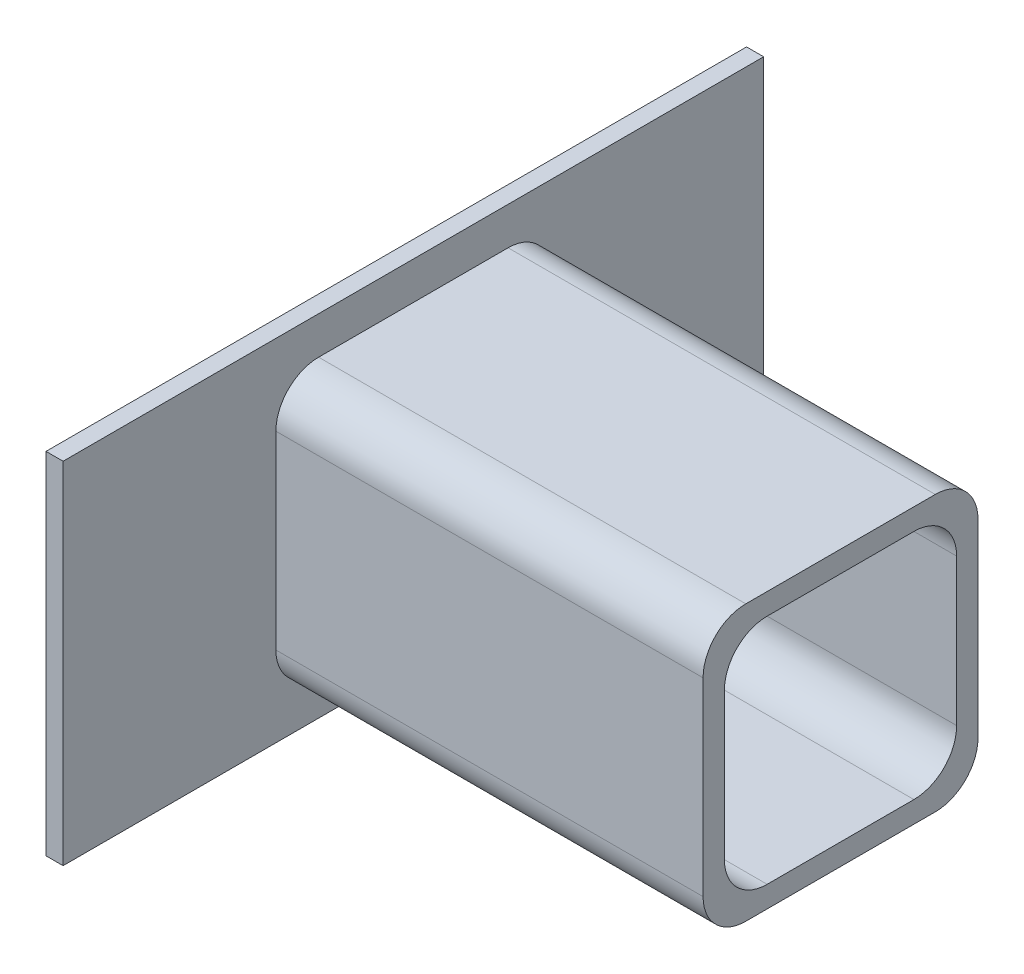
SolidWorks part; units mm, degrees
material "6061 Alloy"
ref_plane "Front Plane" through (0, 0, 0) normal (0, 0, 1) x (1, 0, 0)
ref_plane "Top Plane" through (0, 0, 0) normal (0, 1, 0) x (1, 0, 0)
ref_plane "Right Plane" through (0, 0, 0) normal (1, 0, 0) x (0, 0, -1)
sketch "Sketch1" plane through (0, 0, 0) normal (1, 0, 0) x (0, 0, -1)
  line L1 (-82, -41) -> (82, -41)
  line L2 (-82, -41) -> (-82, 41)
  line L3 (-82, 41) -> (82, 41)
  line L4 (82, -41) -> (82, 41)
  line L5 (-82, -41) -> (82, 41) construction
  line L6 (-82, 41) -> (82, -41) construction
  point P0 (0, 0)
  dimension "D1" = 82
  dimension "D2" = 164
extrude "Boss-Extrude1" add sketch "Sketch1" along normal blind 4
sketch "Sketch7" plane through (4, 0, 0) normal (1, 0, 0) x (0, 0, -1)
  line L1 (-17.18, -27.18) -> (17.18, -27.18)
  line L2 (-27.18, -17.18) -> (-27.18, 17.18)
  line L3 (-17.18, 27.18) -> (17.18, 27.18)
  line L4 (27.18, -17.18) -> (27.18, 17.18)
  line L5 (-27.18, -27.18) -> (27.18, 27.18) construction
  line L6 (-27.18, 27.18) -> (27.18, -27.18) construction
  line L7 (-22.18, -32.18) -> (22.18, -32.18)
  line L8 (-32.18, -22.18) -> (-32.18, 22.18)
  line L9 (-22.18, 32.18) -> (22.18, 32.18)
  line L10 (32.18, -22.18) -> (32.18, 22.18)
  line L11 (-32.18, -32.18) -> (32.18, 32.18) construction
  line L12 (-32.18, 32.18) -> (32.18, -32.18) construction
  arc A0 (22.18, -32.18) -> (32.18, -22.18) centre (22.18, -22.18) ccw
  arc A1 (22.18, 32.18) -> (32.18, 22.18) centre (22.18, 22.18) cw
  arc A2 (-32.18, 22.18) -> (-22.18, 32.18) centre (-22.18, 22.18) cw
  arc A3 (-22.18, -32.18) -> (-32.18, -22.18) centre (-22.18, -22.18) cw
  arc A4 (-17.18, -27.18) -> (-27.18, -17.18) centre (-17.18, -17.18) cw
  arc A5 (17.18, -27.18) -> (27.18, -17.18) centre (17.18, -17.18) ccw
  arc A6 (17.18, 27.18) -> (27.18, 17.18) centre (17.18, 17.18) cw
  arc A7 (-27.18, 17.18) -> (-17.18, 27.18) centre (-17.18, 17.18) cw
  point P0 (0, 0)
  point P6 (0, 0)
  dimension "D5" = 10
  dimension "D1" = 54.36
  dimension "D2" = 54.36
  dimension "D3" = 5
  dimension "D4" = 5
extrude "Boss-Extrude5" add sketch "Sketch7" along normal blind 100
